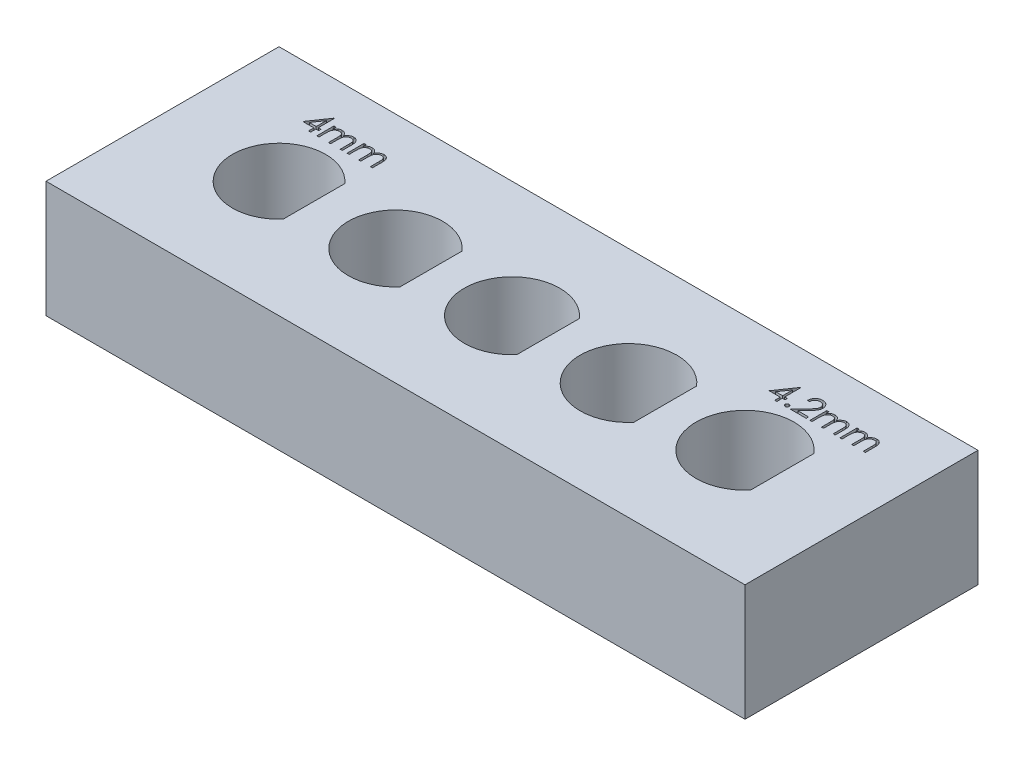
SolidWorks part; units mm, degrees
material "ABS"
ref_plane "Front Plane" through (0, 0, 0) normal (0, 0, 1) x (1, 0, 0)
ref_plane "Top Plane" through (0, 0, 0) normal (0, 1, 0) x (1, 0, 0)
ref_plane "Right Plane" through (0, 0, 0) normal (1, 0, 0) x (0, 0, -1)
sketch "Sketch1" plane through (0, 0, 0) normal (0, 1, 0) x (1, 0, 0)
  line L0 (-10, 0) -> (-15, 0) construction
  line L1 (0, -5) -> (0, 5) construction
  line L2 (-15, 5) -> (15, 5)
  line L3 (-15, 5) -> (-15, -5)
  line L4 (-15, -5) -> (15, -5)
  line L5 (15, 5) -> (15, -5)
  line L6 (-10, 0) -> (-5, 0) construction
  line L7 (-10, -2) -> (-10, 2) construction
  line L8 (-10, 0) -> (-12, 0)
  line L9 (-8.5, 1.3229) -> (-8.5, -1.3229)
  line L10 (-5, 0) -> (0, 0) construction
  line L11 (-5, -2.025) -> (-5, 2.025) construction
  line L12 (-5, 0) -> (-7.025, 0)
  line L13 (-3.475, 1.3323) -> (-3.475, -1.3323)
  line L14 (0, 0) -> (5, 0) construction
  line L15 (0, -2.05) -> (0, 2.05) construction
  line L16 (0, 0) -> (-2.05, 0)
  line L17 (1.55, 1.3416) -> (1.55, -1.3416)
  line L18 (5, 0) -> (10, 0) construction
  line L19 (5, -2.075) -> (5, 2.075) construction
  line L20 (5, 0) -> (2.925, 0)
  line L21 (6.575, 1.3509) -> (6.575, -1.3509)
  line L22 (10, 0) -> (21.9024, 0) construction
  line L23 (10, -2.1) -> (10, 2.1) construction
  line L24 (10, 0) -> (7.9, 0)
  line L25 (11.6, 1.3601) -> (11.6, -1.3601)
  arc A0 (-8.5, 1.3229) -> (-8.5, -1.3229) centre (-10, 0) ccw
  arc A1 (-3.475, 1.3323) -> (-3.475, -1.3323) centre (-5, 0) ccw
  arc A2 (1.55, 1.3416) -> (1.55, -1.3416) centre (0, 0) ccw
  arc A3 (6.575, 1.3509) -> (6.575, -1.3509) centre (5, 0) ccw
  arc A4 (11.6, 1.3601) -> (11.6, -1.3601) centre (10, 0) ccw
  dimension "D1" = 30
  dimension "D2" = 10
  dimension "D3" = 3.5
  dimension "D4" = 4
  dimension "D6" = 3.55
  dimension "D7" = 4.05
  dimension "D8" = 3.6
  dimension "D9" = 4.1
  dimension "D10" = 3.65
  dimension "D11" = 4.15
  dimension "D5" = 5
  dimension "D12" = 3.7
  dimension "D13" = 4.2
extrude "Boss-Extrude1" add sketch "Sketch1" against normal blind 5 contours L5 L2 L3 L4 A4 L25 A3 L21 A2 L17 A1 L13 A0 L9
sketch "Sketch2" plane through (0, 0, 0) normal (0, 1, 0) x (1, 0, 0)
  line L0 (-11.7476, 2.5) -> (-8.6067, 2.5) construction
  line L1 (-7.0463, 2.5) -> (-3.3095, 2.5) construction
  line L2 (-1.6714, 2.5) -> (1.6508, 2.5) construction
  line L3 (1.6508, 2.5) -> (3.3567, 2.5) construction
  line L4 (6.8159, 2.5) -> (8.268, 2.5) construction
  line L5 (-15, 5) -> (-15, -5) construction
  line L6 (-8.6067, 2.5) -> (-7.0463, 2.5) construction
  line L7 (-3.3095, 2.5) -> (-1.6714, 2.5) construction
  line L8 (-11.7476, 2.5) -> (-15, 2.5) construction
  line L9 (12.0166, 2.5) -> (15, 2.5) construction
  line L10 (3.3567, 2.5) -> (6.8159, 2.5) construction
  line L11 (8.268, 2.5) -> (12.0166, 2.5) construction
  line L13 (15, 5) -> (15, -5) construction
  text T0 "4mm" font "Century Gothic" height 1
  text T1 "4.2mm" font "Century Gothic" height 1
  point P5 (0, 0)
  dimension "D1" = 2.5
extrude "Cut-Extrude1" cut sketch "Sketch2" against normal blind 0.5
equation "\"D5@Sketch1\"=\"D1@Sketch1\"/6"
